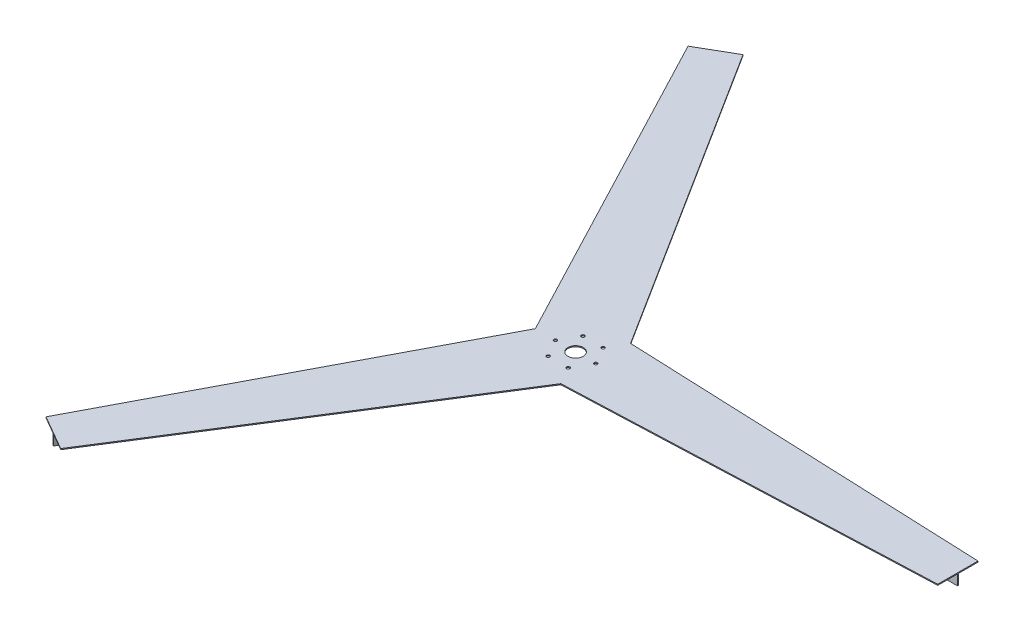
SolidWorks part; units mm, degrees
ref_plane "Alzado" through (0, 0, 0) normal (0, 0, 1) x (1, 0, 0)
ref_plane "Planta" through (0, 0, 0) normal (0, 1, 0) x (1, 0, 0)
ref_plane "Vista lateral" through (0, 0, 0) normal (1, 0, 0) x (0, 0, -1)
sketch "Croquis1" plane through (0, 0, 0) normal (0, 1, 0) x (1, 0, 0)
  line L0 (0, 0) -> (950, 0) construction
  line L1 (-431.6987, -847.7241) -> (-518.3013, -797.7241)
  line L2 (-100, 0) -> (-518.3013, -797.7241)
  line L3 (-431.6987, -847.7241) -> (50, -86.6025)
  line L6 (950, 50) -> (950, -50)
  line L9 (50, 86.6025) -> (0, 0) construction
  line L10 (0, 0) -> (-475, -822.7241) construction
  line L18 (0, 0) -> (50, -86.6025) construction
  line L19 (50, -86.6025) -> (0, 0) construction
  line L20 (0, 0) -> (9.525, 16.4978) construction
  line L22 (50, -86.6025) -> (950, -50)
  line L25 (950, 50) -> (50, 86.6025)
  line L27 (0, 0) -> (-100, 0) construction
  line L28 (-518.3013, 797.7241) -> (-431.6987, 847.7241)
  line L29 (50, 86.6025) -> (-431.6987, 847.7241)
  line L30 (-518.3013, 797.7241) -> (-100, 0)
  line L31 (0, 0) -> (-475, 822.7241) construction
  line L32 (-100, 0) -> (0, 0) construction
  line L33 (0, 0) -> (50, 86.6025) construction
  line L34 (50, 86.6025) -> (50, -86.6025) construction
  circle A0 centre (0, 0) radius 19.05
  point P3 (475, 0)
  point P8 (-237.5, -411.3621)
  point P17 (-237.5, 411.3621)
  point P23 (0, 0)
  point P26 (0, 0)
  dimension "D2" = 38.1
  dimension "D3" = 3
  dimension "D4" = 950
  dimension "D6" = 100
  dimension "D9" = 60
  dimension "D12" = 100
extrude "Saliente-Extruir3" add sketch "Croquis1" along normal blind 2.5
sketch "Croquis2" plane through (0, 0, 0) normal (0, -1, 0) x (1, 0, 0)
  line L0 (950, 0) -> (65, 0) construction
  line L1 (950, -50) -> (950, 50) construction
  line L2 (65, 1.25) -> (65, -1.25)
  line L3 (65, -1.25) -> (950, -1.25)
  line L4 (950, -1.25) -> (950, 1.25)
  line L5 (950, 1.25) -> (65, 1.25)
  line L18 (-473.9175, -823.3491) -> (-31.4175, -56.9167)
  line L22 (-33.5825, -55.6667) -> (-476.0825, -822.0991)
  line L23 (-476.0825, -822.0991) -> (-473.9175, -823.3491)
  line L24 (-475, -822.7241) -> (-32.5, -56.2917) construction
  line L25 (-31.4175, -56.9167) -> (-33.5825, -55.6667)
  line L26 (-476.0825, 822.0991) -> (-33.5825, 55.6667)
  line L27 (-31.4175, 56.9167) -> (-473.9175, 823.3491)
  line L28 (-473.9175, 823.3491) -> (-476.0825, 822.0991)
  line L29 (-475, 822.7241) -> (-32.5, 56.2917) construction
  line L30 (-33.5825, 55.6667) -> (-31.4175, 56.9167)
  point P8 (65, 0)
  point P21 (5, 2.8868)
  point P26 (0, 0)
  dimension "D1" = 885
  dimension "D2" = 2.5
  dimension "D3" = 3
extrude "Saliente-Extruir4" add sketch "Croquis2" along normal blind 25.4
sketch "Croquis4" plane through (0, 2.5, 0) normal (0, 1, 0) x (1, 0, 0)
  line L0 (0, 0) -> (50, 0) construction
  line L1 (50, 0) -> (25, 43.3013) construction
  line L2 (25, 43.3013) -> (-25, 43.3013) construction
  line L3 (-25, 43.3013) -> (-50, 0) construction
  line L4 (-50, 0) -> (-25, -43.3013) construction
  line L5 (-25, -43.3013) -> (25, -43.3013) construction
  line L6 (25, -43.3013) -> (50, 0) construction
  circle A2 centre (0, 0) radius 43.3013 construction
  circle A3 centre (25, -43.3013) radius 4
  circle A4 centre (-25, -43.3013) radius 4
  circle A5 centre (-50, 0) radius 4
  circle A6 centre (-25, 43.3013) radius 4
  circle A7 centre (25, 43.3013) radius 4
  circle A8 centre (50, 0) radius 4
  point P26 (0, 0)
  dimension "D4" = 8
  dimension "D5" = 50
  dimension "D6" = 86.6025
  dimension "D2" = 50
  dimension "D7" = 50
  dimension "D8" = 6
extrude "Cortar-Extruir1" cut sketch "Croquis4" against normal blind 2.54
sketch "Croquis5" plane through (0, 0, 0) normal (0, -1, 0) x (1, 0, 0)
  circle A0 centre (0, 0) radius 19.05
